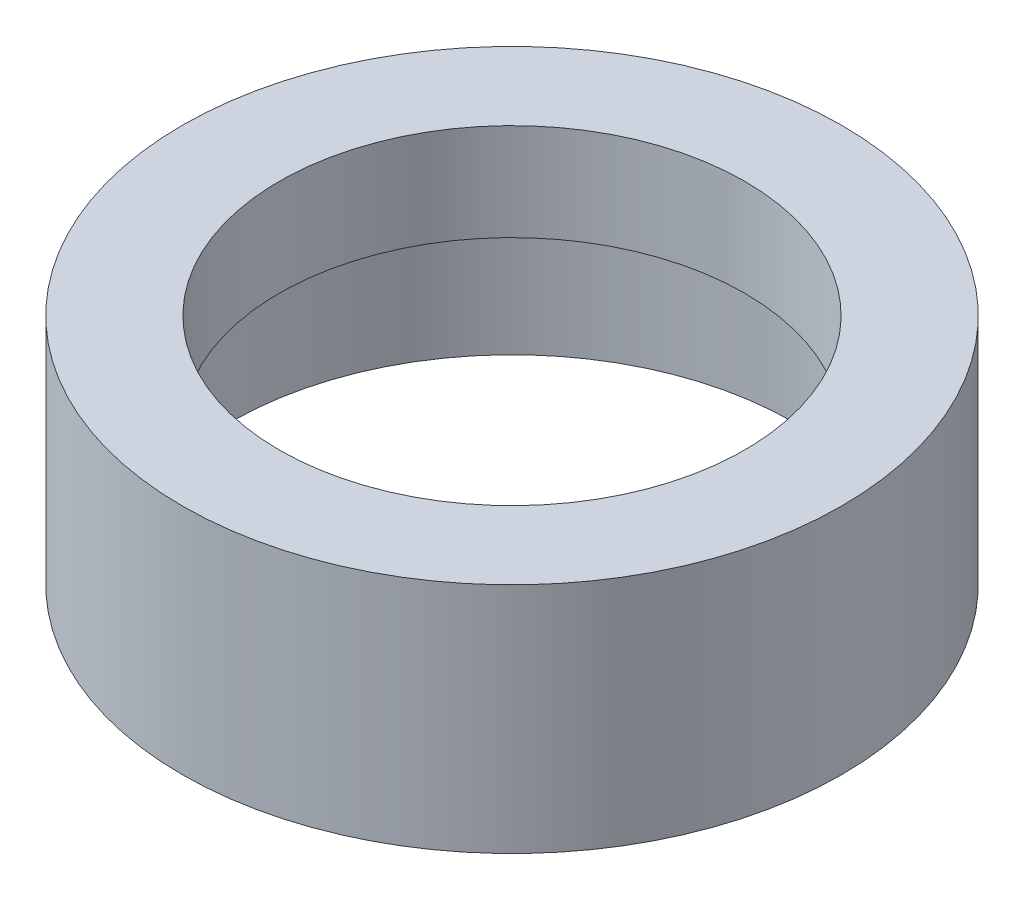
SolidWorks part; units mm, degrees
ref_plane "Plan de face" through (0, 0, 0) normal (0, 0, 1) x (1, 0, 0)
ref_plane "Plan de dessus" through (0, 0, 0) normal (0, 1, 0) x (1, 0, 0)
ref_plane "Plan de droite" through (0, 0, 0) normal (1, 0, 0) x (0, 0, -1)
sketch "Esquisse1" plane through (0, 0, 0) normal (0, 1, 0) x (1, 0, 0)
  circle A0 centre (0, 0) radius 17
  circle A1 centre (0, 0) radius 12
  dimension "D1" = 34
  dimension "D2" = 24
extrude "Boss.-Extru.1" add sketch "Esquisse1" along normal blind 12
sketch "Esquisse2" plane through (0, 0, 0) normal (0, -1, 0) x (1, 0, 0)
  circle A0 centre (0, 0) radius 14.5
  dimension "D1" = 29
extrude "Enlèv. mat.-Extru.1" cut sketch "Esquisse2" against normal blind 7
